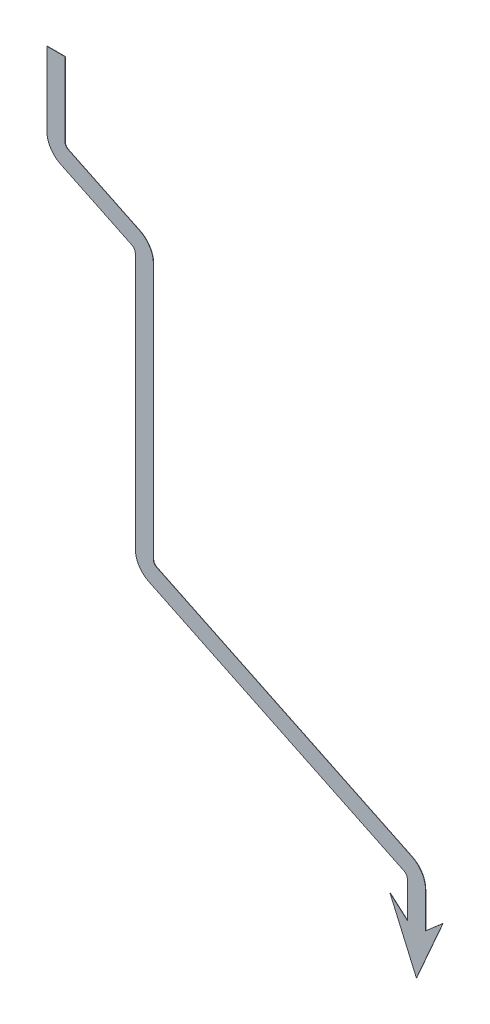
SolidWorks part; units mm, degrees
material "E335"
ref_plane "Plan1" through (0, 0, 0) normal (0, 0, 1) x (1, 0, 0)
ref_plane "Plan2" through (0, 0, 0) normal (0, 1, 0) x (1, 0, 0)
ref_plane "Plan3" through (0, 0, 0) normal (1, 0, 0) x (0, 0, -1)
sketch "Esquisse1" plane through (0, 0, 0) normal (0, 0, 1) x (1, 0, 0)
  line L0 (150.0759, -157.5009) -> (14.0402, -91.9738) construction
  line L1 (134.3181, -165.0912) -> (-21.3884, -90.089) construction
  line L2 (14.0402, -84.4738) -> (14.0402, -91.9738) construction
  line L3 (-21.3884, -81.9738) -> (-21.3884, -90.089) construction
  line L4 (10.8888, -79.3738) -> (10.8888, 79.3738) construction
  line L5 (5.444, -79.3738) -> (5.444, 79.3738) construction
  line L6 (0, -79.3738) -> (0, 79.3738) construction
  line L7 (-5.4444, -79.3738) -> (-5.4444, 79.3738) construction
  line L8 (-10.8892, -79.3738) -> (-10.8892, 79.3738) construction
  line L9 (-16.3332, -79.3738) -> (-16.3332, 79.3738) construction
  line L10 (14.0402, 90.089) -> (14.0402, 84.4738) construction
  line L11 (-26.3806, 109.5592) -> (14.0402, 90.089) construction
  line L12 (-21.3884, 91.9738) -> (-21.3884, 81.9738) construction
  line L13 (-21.3884, 91.9738) -> (-42.1384, 101.9689) construction
sketch "Esquisse2" plane through (0, 0, 0) normal (0, 0, 1) x (1, 0, 0)
  line L0 (-56.3598, 116.4096) -> (-9.1201, 93.6547)
  line L1 (-3.4598, 84.6454) -> (-3.4598, -84.8518)
  line L2 (2.2005, -93.8611) -> (171.0655, -175.2017)
  line L3 (-21.3884, 91.9738) -> (-42.1384, 101.9689) construction
  line L4 (150.0759, -157.5009) -> (14.0402, -91.9738) construction
  line L5 (-6.1702, 99.8241) -> (-9.1379, 93.6632) construction
  line L6 (-26.3806, 109.5592) -> (14.0402, 90.089) construction
  line L7 (-31.7634, 96.9713) -> (-28.7958, 103.1322) construction
  line L8 (82.058, -124.7373) -> (79.0904, -130.8982) construction
  line L10 (56.4648, -127.5901) -> (59.4325, -121.4292) construction
  line L11 (-62.0202, 125.4189) -> (-62.0202, 174.1361)
  line L12 (-21.3884, 81.9738) -> (14.0402, 81.9738) construction
  line L13 (14.0402, 84.4738) -> (14.0402, 81.9738) construction
  line L14 (176.7258, -184.211) -> (176.7258, -207.9282)
  line L15 (134.3181, -165.0912) -> (-21.3884, -90.089) construction
  arc A0 (-3.4598, 84.6454) -> (-9.1201, 93.6547) centre (-13.4598, 84.6454) ccw
  arc A1 (2.2005, -93.8611) -> (-3.4598, -84.8518) centre (6.5402, -84.8518) cw
  arc A2 (176.7258, -184.211) -> (171.0655, -175.2017) centre (166.7258, -184.211) ccw
  arc A3 (-56.3598, 116.4096) -> (-62.0202, 125.4189) centre (-52.0202, 125.4189) cw
  point P30 (-3.4598, 90.9282)
  point P33 (-3.4598, -91.1346)
  point P36 (176.7258, -177.9282)
  point P39 (-62.0202, 119.1361)
  dimension "D5" = 10
  dimension "D1" = 65
  dimension "D2" = 55
  dimension "D3" = 200
  dimension "D4" = 30
  dimension "D6" = 17.5
extrude "Extru.-Mince1" add sketch "Esquisse2" along normal blind 0.2 thin thin type mid plane wall 12
sketch "Esquisse3" plane through (0, 0, 0) normal (0, 0, -1) x (-1, 0, 0)
  line L0 (-182.7258, -207.9282) -> (-194.2258, -197.9282)
  line L1 (-176.7258, -207.9282) -> (-176.7258, -237.9282) construction
  line L2 (-182.7258, -207.9282) -> (-170.7258, -207.9282) construction
  line L3 (-194.2258, -197.9282) -> (-176.7258, -237.9282)
  line L4 (-159.2258, -197.9282) -> (-176.7258, -237.9282)
  line L5 (-170.7258, -207.9282) -> (-159.2258, -197.9282)
  line L6 (-182.7258, -207.9282) -> (-170.7258, -207.9282)
  dimension "D1" = 35
  dimension "D2" = 10
  dimension "D3" = 30
extrude "Extrusion1" add sketch "Esquisse3" against normal up to surface (0.2 mm away) up to face at (33.0278, -15.1789, 0.2)
